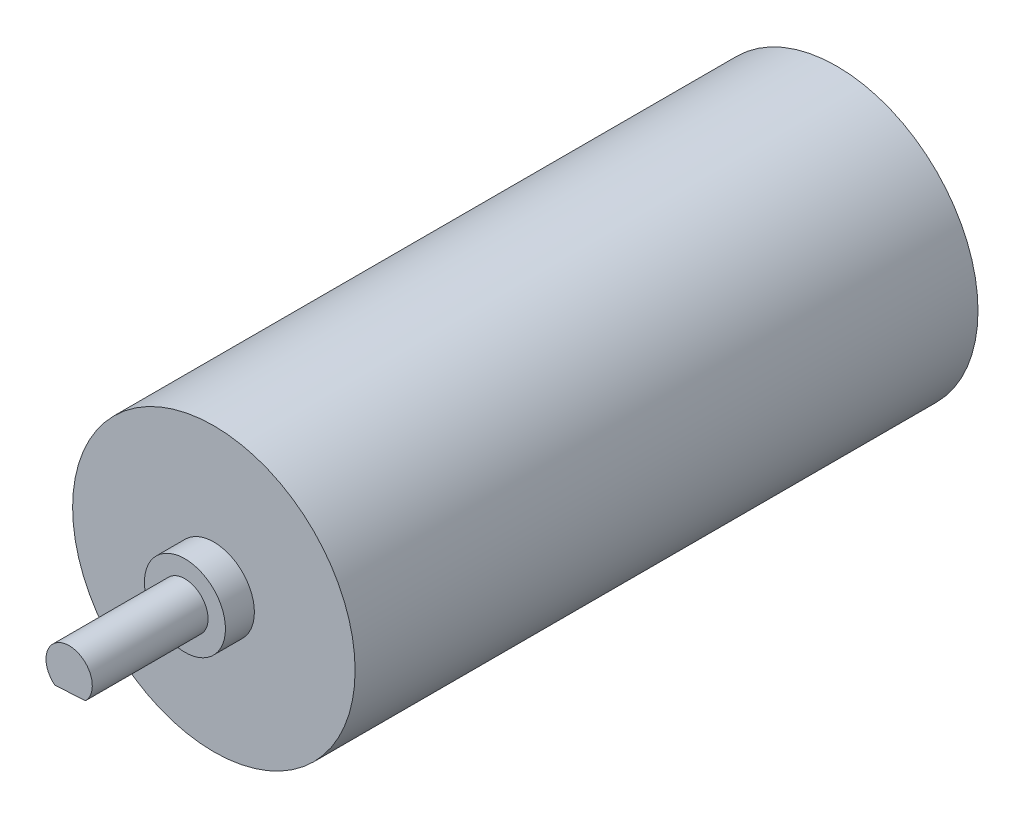
SolidWorks part; units mm, degrees
ref_plane "Front" through (0, 0, 0) normal (0, 0, 1) x (1, 0, 0)
ref_plane "Top" through (0, 0, 0) normal (0, 1, 0) x (1, 0, 0)
ref_plane "Right" through (0, 0, 0) normal (1, 0, 0) x (0, 0, -1)
sketch "Esquisse1" plane through (0, 0, 0) normal (0, 0, 1) x (1, 0, 0)
  circle A0 centre (0, 0) radius 12.2
  dimension "D1" = 24.4
extrude "Boss.-Extru.1" add sketch "Esquisse1" along normal mid plane 53.8
sketch "Esquisse2" plane through (0, 0, 26.9) normal (0, 0, 1) x (1, 0, 0)
  circle A0 centre (0, 0) radius 3.5
  dimension "D1" = 7
extrude "Boss.-Extru.2" add sketch "Esquisse2" along normal blind 2.5
sketch "Esquisse3" plane through (0, 0, 29.4) normal (0, 0, 1) x (1, 0, 0)
  circle A0 centre (0, 0) radius 2
  dimension "D1" = 4
extrude "Boss.-Extru.3" add sketch "Esquisse3" along normal blind 10
sketch "Esquisse4" plane through (0, 0, 39.4) normal (0, 0, 1) x (1, 0, 0)
  line L0 (-1.2338, -1.5741) -> (1.4075, -1.4209)
  arc A0 (-1.2338, -1.5741) -> (1.4075, -1.4209) centre (0, 0) ccw
  circle A1 centre (0, 0) radius 2 construction
  point P6 (0.1158, -1.9966)
  dimension "D1" = 0.5
extrude "Enlèv. mat.-Extru.1" cut sketch "Esquisse4" against normal blind 8
